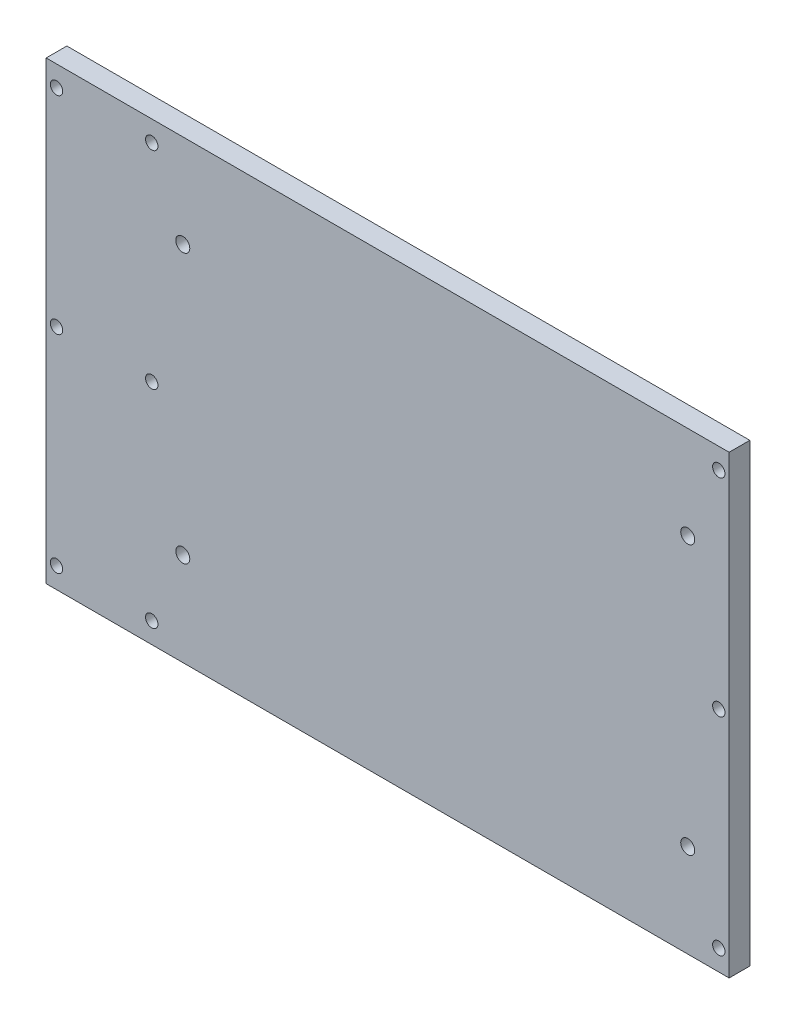
SolidWorks part; units mm, degrees
material "1060 Alloy"
ref_plane "Front Plane" through (0, 0, 0) normal (0, 0, 1) x (1, 0, 0)
ref_plane "Top Plane" through (0, 0, 0) normal (0, 1, 0) x (1, 0, 0)
ref_plane "Right Plane" through (0, 0, 0) normal (1, 0, 0) x (0, 0, -1)
sketch "Sketch1" plane through (0, 0, 0) normal (0, 0, 1) x (1, 0, 0)
  line L6 (104.775, 69.85) -> (-104.775, 69.85)
  line L9 (104.775, 69.85) -> (104.775, -69.85)
  line L10 (104.775, -69.85) -> (-104.775, -69.85)
  line L11 (-104.775, 69.85) -> (-104.775, -69.85)
  line L12 (104.775, 69.85) -> (-104.775, -69.85) construction
  line L13 (104.775, -69.85) -> (-104.775, 69.85) construction
  point P0 (0, 0)
  dimension "D1" = 139.7
  dimension "D2" = 209.55
extrude "Boss-Extrude1" add sketch "Sketch1" along normal mid plane 6.35
other "Cavity1"
other "Face_Plate<2>@Shredder1"
other "Face_Plate<1>@Shredder1"
other "Face_Plate<3>@Shredder1"
hole_wizard "#6 Clearance Hole1" positions "Sketch2" profile "Sketch3" hole size "#6" standard "ANSI Inch"
sketch "Sketch2" plane through (0, 0, 3.175) normal (0, 0, 1) x (1, 0, 0)
  point P0 (-62.865, 41.275)
  point P3 (92.075, 41.275)
  point P6 (92.075, -41.275)
  point P9 (-62.865, -41.275)
sketch "Sketch3" plane through (-62.865, 41.275, 3.175) normal (1, 0, 0) x (0, -1, 0)
  line L0 (0, 0) -> (0, 10.9454)
  line L1 (0, 10.9454) -> (2.1526, 9.652)
  line L2 (2.1526, 9.652) -> (2.1526, 0)
  line L5 (2.1526, 0) -> (0, 0)
  line L10 (0, 10.9454) -> (-2.1527, 9.652) construction
  line L11 (0, -6.35) -> (0, 107.95) construction
  dimension "Hole Dia." = 4.3053
  dimension "Hole Depth" = 9.652
  dimension "Drill Angle" = 118
hole_wizard "#6 Clearance Hole2" positions "Sketch4" profile "Sketch5" hole size "#6" standard "ANSI Inch" end condition through all
sketch "Sketch4" plane through (0, 0, -3.175) normal (0, 0, -1) x (-1, 0, 0)
  line L1 (-104.775, -69.85) -> (-104.775, 69.85) construction
  line L2 (104.775, 69.85) -> (104.775, -69.85) construction
  point P0 (-101.6, 63.5)
  point P2 (-101.6, 0)
  point P4 (-101.6, -63.5)
  point P6 (72.39, 63.5)
  point P8 (72.39, 0)
  point P10 (72.39, -63.5)
  point P12 (101.6, -63.5)
  point P14 (101.6, 0)
  point P16 (101.6, 63.5)
  dimension "D1" = 3.175
  dimension "D2" = 63.5
  dimension "D3" = 63.5
  dimension "D4" = 3.175
  dimension "D5" = 32.385
sketch "Sketch5" plane through (101.6, 63.5, -3.175) normal (1, 0, 0) x (0, 1, 0)
  line L0 (0, 0) -> (0, 6.35)
  line L1 (0, 6.35) -> (1.8986, 6.35)
  line L2 (1.8986, 6.35) -> (1.8986, 0.635)
  line L3 (1.8986, 0.635) -> (2.5337, 0)
  line L5 (2.5337, 0) -> (0, 0)
  line L6 (-1.8986, 0.635) -> (-2.5337, 0) construction
  line L11 (0, -6.35) -> (0, 107.95) construction
  dimension "Thru Hole Dia." = 3.7973
  dimension "Thru Hole Depth" = 6.35
  dimension "Near C'Sink Dia." = 5.0673
  dimension "Near C'Sink Angle" = 90
equation "\"thicc\"= .25"
equation "\"D1@Sketch4\"=\"thicc\"/2"
equation "\"hole_dist\"=2.5"
equation "\"D2@Sketch4\"=\"hole_dist\""
equation "\"D3@Sketch4\"=\"hole_dist\""
equation "\"D4@Sketch4\"=\"thicc\"/2"
equation "\"D5@Sketch4\"=1.15 + .5*\"thicc\""
